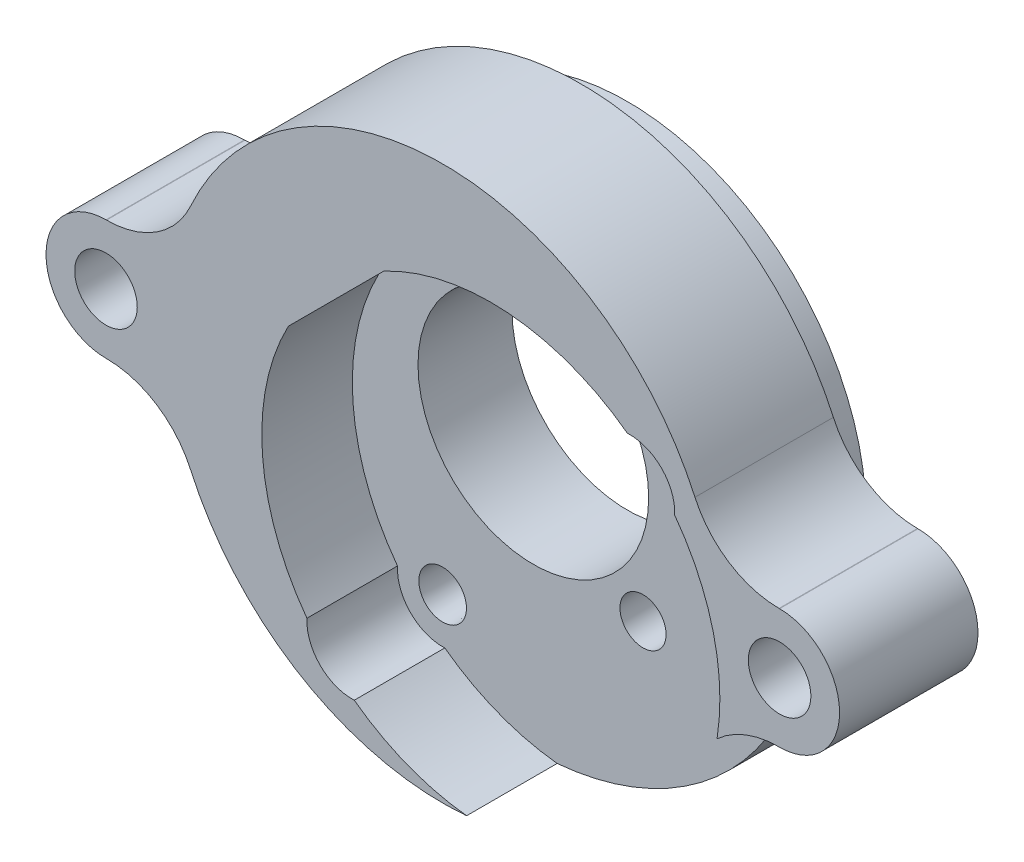
SolidWorks part; units mm, degrees
material "PET"
ref_plane "Front" through (0, 0, 0) normal (0, 0, 1) x (1, 0, 0)
ref_plane "Top" through (0, 0, 0) normal (0, 1, 0) x (1, 0, 0)
ref_plane "Right" through (0, 0, 0) normal (1, 0, 0) x (0, 0, -1)
sketch "Sketch1" plane through (0, 0, 0) normal (0, 0, 1) x (1, 0, 0)
  line L0 (23.1775, 2.8575) -> (16.1706, 2.8575)
  line L1 (23.1775, -2.8575) -> (16.1706, -2.8575)
  line L2 (0, 16.4211) -> (0, -16.4211) construction
  line L3 (-23.1775, -2.8575) -> (-16.1706, -2.8575)
  line L4 (-23.1775, 2.8575) -> (-16.1706, 2.8575)
  circle A0 centre (0, 0) radius 16.4211 construction
  arc A1 (16.1706, 2.8575) -> (-16.1706, 2.8575) centre (0, 0) ccw
  circle A3 centre (0, 0) radius 7.9375
  arc A4 (-16.1706, -2.8575) -> (16.1706, -2.8575) centre (0, 0) ccw
  arc A5 (23.1775, -2.8575) -> (23.1775, 2.8575) centre (23.1775, 0) ccw
  arc A6 (23.1775, -2.8575) -> (23.1775, 2.8575) centre (23.1775, 0) ccw
  arc A7 (-23.1775, -2.8575) -> (-23.1775, 2.8575) centre (-23.1775, 0) cw
  arc A8 (-16.1706, 2.8575) -> (-16.1706, -2.8575) centre (0, 0) ccw
  arc A9 (16.1706, 2.8575) -> (16.1706, -2.8575) centre (0, 0) cw
  dimension "D2" = 15.875
  dimension "D1" = 1.27
extrude "Boss-Extrude1" add sketch "Sketch1" along normal blind 6.35 contours L2 A1 A8 A4 A3 | A1 L2 A3 A4 A9
sketch "Sketch2" plane through (0, 0, 6.35) normal (0, 0, 1) x (1, 0, 0)
  line L4 (23.1775, 4.1275) -> (23.1383, 4.1275)
  line L5 (-23.1383, 4.1275) -> (-23.1775, 4.1275)
  line L6 (-23.1775, -4.1275) -> (-23.1383, -4.1275)
  line L7 (23.1383, -4.1275) -> (23.1775, -4.1275)
  line L8 (23.1775, 4.1275) -> (23.1383, 4.1275)
  line L9 (-23.1383, 4.1275) -> (-23.1775, 4.1275)
  line L10 (-23.1775, -4.1275) -> (-23.1383, -4.1275)
  line L11 (23.1383, -4.1275) -> (23.1775, -4.1275)
  circle A1 centre (0, 0) radius 16.4211
  circle A2 centre (0, 0) radius 16.4211
  arc A8 (17.3537, 7.8581) -> (23.1383, 4.1275) centre (23.1383, 10.4775) ccw
  arc A9 (17.3537, 7.8581) -> (-17.3537, 7.8581) centre (0, 0) ccw
  arc A10 (-23.1383, 4.1275) -> (-17.3537, 7.8581) centre (-23.1383, 10.4775) ccw
  arc A11 (-23.1775, 4.1275) -> (-23.1775, -4.1275) centre (-23.1775, 0) ccw
  arc A12 (-17.3537, -7.8581) -> (-23.1383, -4.1275) centre (-23.1383, -10.4775) ccw
  arc A13 (-17.3537, -7.8581) -> (17.3537, -7.8581) centre (0, 0) ccw
  arc A14 (23.1383, -4.1275) -> (17.3537, -7.8581) centre (23.1383, -10.4775) ccw
  arc A15 (23.1775, -4.1275) -> (23.1775, 4.1275) centre (23.1775, 0) ccw
  arc A16 (17.3537, 7.8581) -> (23.1383, 4.1275) centre (23.1383, 10.4775) ccw
  arc A17 (17.3537, 7.8581) -> (-17.3537, 7.8581) centre (0, 0) ccw
  arc A18 (-23.1383, 4.1275) -> (-17.3537, 7.8581) centre (-23.1383, 10.4775) ccw
  arc A19 (-23.1775, 4.1275) -> (-23.1775, -4.1275) centre (-23.1775, 0) ccw
  arc A20 (-17.3537, -7.8581) -> (-23.1383, -4.1275) centre (-23.1383, -10.4775) ccw
  arc A21 (-17.3537, -7.8581) -> (17.3537, -7.8581) centre (0, 0) ccw
  arc A22 (23.1383, -4.1275) -> (17.3537, -7.8581) centre (23.1383, -10.4775) ccw
  arc A23 (23.1775, -4.1275) -> (23.1775, 4.1275) centre (23.1775, 0) ccw
  dimension "D1" = 0
  dimension "D2" = 0
extrude "Boss-Extrude3" add sketch "Sketch2" against normal blind 3.175 and the other way blind 6.35
hole_wizard "#6 Clearance Hole1" positions "Sketch21" profile "Sketch3" hole size "#6" standard "ANSI Inch" end condition up to next
sketch "Sketch21" plane through (-22.6996, 0.1044, 3.175) normal (0, 0, -1) x (-1, 0, 0)
  point P0 (-45.8771, -0.1044)
  point P3 (0.4779, -0.1044)
sketch "Sketch3" plane through (23.1775, 0, 3.175) normal (1, 0, 0) x (0, 1, 0)
  line L0 (0, 0) -> (0, 9.525)
  line L1 (0, 9.525) -> (2.1526, 9.525)
  line L2 (2.1526, 9.525) -> (2.1526, 0)
  line L5 (2.1526, 0) -> (0, 0)
  line L11 (0, -6.35) -> (0, 107.95) construction
  dimension "Thru Hole Dia." = 4.3053
  dimension "Thru Hole Depth" = 9.525
hole_wizard "#6 Plastic Insert" positions "Sketch4" profile "Sketch5" legacy
sketch "Sketch4" plane through (-45.3006, 0, 3.175) normal (0, 0, -1) x (-1, 0, 0)
  point P0 (-68.4781, 0)
  point P3 (-22.1231, 0)
sketch "Sketch5" plane through (23.1775, 0, 3.175) normal (1, 0, 0) x (0, 1, 0)
  line L0 (0, 0) -> (0, 3.81)
  line L1 (0, 3.81) -> (2.5273, 3.81)
  line L2 (2.5273, 3.81) -> (2.6543, 0)
  line L3 (2.6543, 0) -> (0, 0)
  line L4 (0, 110) -> (0, -10) construction
  dimension "Minor Diameter" = 5.0546
  dimension "Depth" = 3.81
  dimension "Major Diameter" = 5.3086
other "#6 Plastic Insert Hole<1>"
sketch "Sketch22" plane through (0, 0, 12.7) normal (0, 0, 1) x (1, 0, 0)
  circle A0 centre (0, 0) radius 7.9375 construction
  circle A1 centre (0, 0) radius 16.4211 construction
  circle A2 centre (0, 0) radius 7.9375
  circle A3 centre (0, 0) radius 16.4211
extrude "Boss-Extrude4" add sketch "Sketch22" against normal up to next
sketch "Sketch23" plane through (0, 0, 12.7) normal (0, 0, 1) x (1, 0, 0)
  line L0 (-4.0603, 10.6294) -> (-10.6294, 4.0603)
  line L1 (-3.6037, 10.0083) -> (-10.0083, 3.6037)
  line L2 (-3.6037, 10.0083) -> (-10.0083, 3.6037) construction
  arc A0 (-10.6294, 4.0603) -> (-9.3488, -12.7028) centre (3.3056, -3.3056) ccw
  circle A1 centre (-6.2403, -12.8516) radius 2.35
  arc A2 (-8.5609, -12.4809) -> (-5.8697, -15.1721) centre (-6.2403, -12.8516) ccw construction
  circle A3 centre (12.8516, 6.2403) radius 2.35
  arc A4 (15.1721, 5.8697) -> (12.4809, 8.5609) centre (12.8516, 6.2403) ccw construction
  arc A5 (-5.8697, -15.1721) -> (-8.5609, -12.4809) centre (-6.2403, -12.8516) ccw
  arc A6 (-5.8697, -15.1721) -> (15.1721, 5.8697) centre (3.3056, -3.3056) ccw
  arc A7 (12.4809, 8.5609) -> (15.1721, 5.8697) centre (12.8516, 6.2403) ccw
  arc A8 (12.4809, 8.5609) -> (-3.6037, 10.0083) centre (3.3056, -3.3056) ccw
  arc A9 (-10.0083, 3.6037) -> (-8.5609, -12.4809) centre (3.3056, -3.3056) ccw
  arc A11 (-5.8697, -15.1721) -> (15.1721, 5.8697) centre (3.3056, -3.3056) ccw construction
  arc A13 (12.4809, 8.5609) -> (-3.6037, 10.0083) centre (3.3056, -3.3056) ccw construction
  arc A14 (-10.0083, 3.6037) -> (-8.5609, -12.4809) centre (3.3056, -3.3056) ccw construction
  arc A15 (-9.3488, -12.7028) -> (-6.0916, -15.96) centre (-6.2403, -12.8516) ccw
  arc A16 (-6.0916, -15.96) -> (15.96, 6.0916) centre (3.3056, -3.3056) ccw
  arc A17 (15.96, 6.0916) -> (12.7028, 9.3488) centre (12.8516, 6.2403) ccw
  arc A18 (12.7028, 9.3488) -> (-4.0603, 10.6294) centre (3.3056, -3.3056) ccw
  dimension "D1" = 0
  dimension "D2" = 0
  dimension "D3" = 0
  dimension "D4" = 0.762
extrude "Cut-Extrude1" cut sketch "Sketch23" against normal up to surface (6.23 mm away)
sketch "Sketch24" plane through (0, 0, 0) normal (0, 0, -1) x (-1, 0, 0)
  circle A0 centre (-7.5483, -7.5483) radius 1.5875
  dimension "D1" = 3.175
extrude "Cut-Extrude2" cut sketch "Sketch24" against normal through all
hole_wizard "Hole1" positions "Sketch25" profile "Sketch26" legacy
sketch "Sketch25" plane through (0, 0, 6.47) normal (0, 0, 1) x (1, 0, 0)
  point P0 (-6.2403, -12.8516)
  point P3 (12.8516, 6.2403)
sketch "Sketch26" plane through (-6.2403, -12.8516, 6.47) normal (1, 0, 0) x (0, -1, 0)
  line L0 (0, 0) -> (0, 2.921)
  line L1 (0, 2.921) -> (1.4986, 2.921)
  line L2 (1.4986, 2.921) -> (1.6383, 0)
  line L3 (1.6383, 0) -> (0, 0)
  line L4 (0, 110) -> (0, -10) construction
  dimension "Minor Diameter" = 2.9972
  dimension "Depth" = 2.921
  dimension "Major Diameter" = 3.2766
hole_wizard "#0 Clearance Hole1" positions "Sketch27" profile "Sketch28" hole size "#0" standard "ANSI Inch" end condition through all
sketch "Sketch27" plane through (0, 0, 6.47) normal (0, 0, 1) x (1, 0, 0)
  point P0 (-6.2403, -12.8516)
  point P3 (12.8516, 6.2403)
sketch "Sketch28" plane through (-6.2403, -12.8516, 6.47) normal (1, 0, 0) x (0, -1, 0)
  line L0 (0, 0) -> (0, 6.47)
  line L1 (0, 6.47) -> (0.9271, 6.47)
  line L2 (0.9271, 6.47) -> (0.9271, 0)
  line L5 (0.9271, 0) -> (0, 0)
  line L11 (0, -6.35) -> (0, 107.95) construction
  dimension "Thru Hole Dia." = 1.8542
  dimension "Thru Hole Depth" = 6.47
